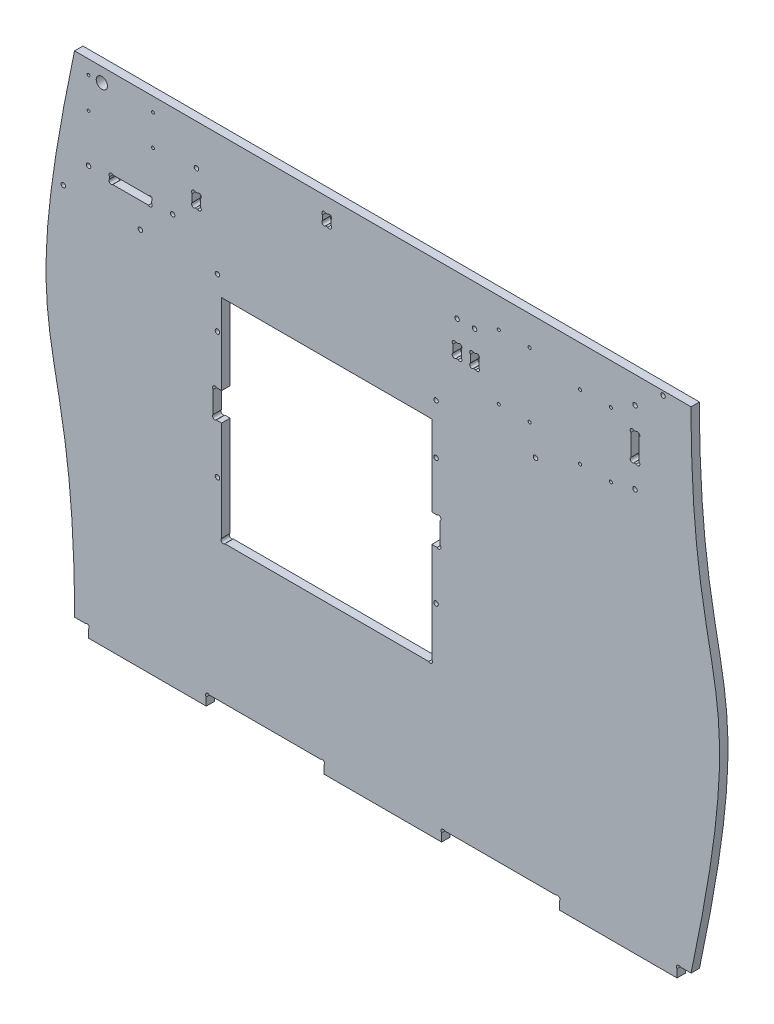
SolidWorks part; units mm, degrees
ref_plane "Plan de face" through (0, 0, 0) normal (0, 0, 1) x (1, 0, 0)
ref_plane "Plan de dessus" through (0, 0, 0) normal (0, 1, 0) x (1, 0, 0)
ref_plane "Plan de droite" through (0, 0, 0) normal (1, 0, 0) x (0, 0, -1)
sketch "Esquisse1" plane through (0, 0, 0) normal (0, 0, 1) x (1, 0, 0)
  line L0 (536.5085, 0) -> (-13.3743, 0) construction
  line L1 (0, 0) -> (84, 0)
  line L2 (0, 8) -> (-13.4384, -5.4384) construction
  line L3 (-10, 358) -> (430, 358)
  line L4 (-10, 8) -> (-2.2627, 8)
  line L5 (0, 317.0008) -> (0, 420.4252) construction
  line L6 (420, -67.8064) -> (420, 420.4252) construction
  line L7 (-58.7504, 358) -> (536.5085, 358) construction
  line L8 (-44.4443, 8) -> (504.1642, 8) construction
  line L9 (-58.7504, 183) -> (504.1642, 183) construction
  line L10 (210, -34.4525) -> (210, 403.8703) construction
  line L11 (95, 312.8184) -> (95, 62.6795) construction
  line L12 (245, 312.8184) -> (245, 77.601) construction
  line L13 (44.0199, 268) -> (294.4824, 268) construction
  line L14 (37.67, 113) -> (257.0223, 113) construction
  line L15 (170, 374.1921) -> (170, 173.0003) construction
  line L16 (377.3817, 329) -> (337.8551, 329) construction
  line L17 (-22.7237, 274) -> (398.8212, 274) construction
  line L18 (61.9408, 190.5) -> (173.6524, 190.5) construction
  line L19 (61.9408, 180.5) -> (97.9919, 180.5) construction
  line L20 (89, 328.4277) -> (89, 62.6795) construction
  line L21 (89, 180.5) -> (106.3802, 197.8802) construction
  line L22 (112.0092, 188) -> (81.9912, 188) construction
  line L23 (434.3285, 271) -> (12.2974, 271) construction
  line L24 (332.75, 372.1626) -> (332.75, 320.7373) construction
  line L25 (61.9408, 145.5) -> (97.9919, 145.5) construction
  line L26 (92, 278.6686) -> (92, 94.6559) construction
  line L27 (112.0092, 284) -> (81.9912, 284) construction
  line L28 (372.75, 339) -> (372.75, 276.9465) construction
  line L29 (91.2627, 180.5) -> (95, 180.5)
  line L30 (95, 180.5) -> (95, 109.2627)
  line L31 (95, 200.5) -> (95, 258)
  line L32 (91.2627, 200.5) -> (95, 200.5)
  line L33 (89, 198.2373) -> (89, 182.7627)
  line L34 (350.75, 339) -> (350.75, 276.9465) construction
  line L35 (174.5986, 347.4) -> (148.3113, 347.4) construction
  line L36 (321.3988, 283) -> (377.3817, 283) construction
  line L37 (251, 198.2373) -> (251, 182.7627)
  line L38 (248.7373, 200.5) -> (245, 200.5)
  line L39 (245, 200.5) -> (245, 258)
  line L40 (245, 180.5) -> (245, 109.2627)
  line L41 (248.7373, 180.5) -> (245, 180.5)
  line L42 (37.67, 107) -> (257.0223, 107) construction
  line L43 (97.2627, 107) -> (242.7373, 107)
  line L44 (84, 13.5522) -> (84, -67.8064) construction
  line L45 (168, 13.5522) -> (168, -67.8064) construction
  line L46 (126, 13.5522) -> (126, -34.4525) construction
  line L47 (84, 8) -> (114.9336, -22.9336) construction
  line L48 (86.2627, 8) -> (165.7373, 8)
  line L49 (84, 5.7373) -> (84, 0)
  line L50 (168, 5.7373) -> (168, 0)
  line L51 (252, 5.7373) -> (252, 0)
  line L52 (168, 0) -> (252, 0)
  line L53 (336, 5.7373) -> (336, 0)
  line L54 (333.7373, 8) -> (254.2627, 8)
  line L55 (336, 0) -> (420, 0)
  line L56 (-18, 278.6686) -> (-18, 232.7276) construction
  line L57 (377.3817, 339) -> (411.7088, 339) construction
  line L58 (319, 282.5821) -> (319, 262.0427) construction
  line L59 (-30, -67.8064) -> (-30, 412.0672) construction
  line L60 (-10, 374.1921) -> (-10, -22.9336) construction
  line L61 (-20, 196.1893) -> (-20, 121.5026) construction
  line L62 (314.75, 339) -> (314.75, 276.9465) construction
  line L63 (-44.4443, 158) -> (15.8377, 158) construction
  line L64 (-58.7504, 208) -> (12.2974, 208) construction
  line L65 (292.75, 339) -> (292.75, 276.9465) construction
  line L66 (420, 0) -> (420, 5.7373)
  line L67 (422.2627, 8) -> (430, 8)
  line L68 (420, 8) -> (436.9027, -8.9027) construction
  line L69 (0, 5.7373) -> (0, 0)
  line L70 (401.9564, 323) -> (377.3817, 323) construction
  line L71 (377.3817, 303) -> (411.7088, 303) construction
  line L72 (377.3817, 287) -> (411.7088, 287) construction
  line L73 (382.8422, 313) -> (400.9535, 313) construction
  line L74 (37, 278.6686) -> (37, 252.4818) construction
  line L75 (387, 265.7773) -> (387, 372.1626) construction
  line L76 (393, 297.0582) -> (393, 363.8775) construction
  line L77 (387, 303) -> (396.2728, 312.2728) construction
  line L78 (389.2627, 323) -> (390.7373, 323)
  line L79 (393, 320.7373) -> (393, 305.2627)
  line L80 (430, 429.0413) -> (430, 142.9931) construction
  line L81 (390, 390.6781) -> (390, 264.55) construction
  line L82 (390.7373, 303) -> (389.2627, 303)
  line L83 (387, 305.2627) -> (387, 320.7373)
  line L84 (95, 107) -> (145.4679, 157.4679) construction
  line L85 (260, 337.0041) -> (260, 279.8872) construction
  line L86 (266, 337.0041) -> (266, 279.8872) construction
  line L87 (282.4812, 304) -> (255.0884, 304) construction
  line L88 (410, 378.6044) -> (410, 349.1334) construction
  line L89 (404.9347, 355) -> (382.8422, 355) construction
  line L90 (-13.3743, 348) -> (53.3664, 348) construction
  line L91 (46, 356.0435) -> (46, 317.0008) construction
  line L92 (9.5, 333.4562) -> (9.5, 351.4952) construction
  line L93 (-13.3743, 326) -> (53.3664, 326) construction
  line L94 (329.6726, 291) -> (286.3117, 291) construction
  line L95 (286.3117, 337) -> (329.6726, 337) construction
  line L96 (257.0223, 258) -> (81.9912, 258) construction
  line L97 (263, 294.766) -> (263, 346.378) construction
  line L98 (282.4812, 309) -> (255.0884, 309) construction
  line L99 (260, 304) -> (273.0008, 317.0008) construction
  line L100 (282.4812, 329) -> (255.0884, 329) construction
  line L101 (262.2627, 314) -> (263.7373, 314)
  line L102 (260, 311.7373) -> (260, 306.2627)
  line L103 (262.2627, 304) -> (263.7373, 304)
  line L104 (266, 306.2627) -> (266, 311.7373)
  line L105 (74, 306.2627) -> (74, 311.7373)
  line L106 (77.7373, 304) -> (76.2627, 304)
  line L107 (80, 311.7373) -> (80, 306.2627)
  line L108 (77.7373, 314) -> (76.2627, 314)
  line L109 (269.25, 337.0041) -> (269.25, 319.1195) construction
  line L110 (272.5, 306.2627) -> (272.5, 311.7373)
  line L111 (276.2373, 304) -> (274.7627, 304)
  line L112 (278.5, 311.7373) -> (278.5, 306.2627)
  line L113 (276.2373, 314) -> (274.7627, 314)
  line L114 (-27.2619, 295) -> (81.9912, 295) construction
  line L115 (73, 282.5821) -> (73, 374.1921) construction
  line L116 (-27.2619, 289) -> (81.9912, 289) construction
  line L117 (30, 312.8686) -> (30, 284) construction
  line L118 (45, 309) -> (45, 284) construction
  line L119 (45, 289) -> (31.8516, 302.1484) construction
  line L120 (60, 309) -> (60, 284) construction
  line L121 (68.4592, 292) -> (52.4653, 292) construction
  line L122 (15, 292.7373) -> (15, 291.2627)
  line L123 (17.2627, 295) -> (42.7373, 295)
  line L124 (17.2627, 289) -> (42.7373, 289)
  line L125 (45, 292.7373) -> (45, 291.2627)
  line L126 (245, 258) -> (95, 258)
  line L127 (174.5986, 343.4) -> (148.3113, 343.4) construction
  line L128 (173, 349.9561) -> (173, 335.0973) construction
  line L129 (173, 347.4) -> (162.419, 336.819) construction
  line L130 (170.7373, 339.4) -> (169.2627, 339.4)
  line L131 (167, 341.6627) -> (167, 345.1373)
  line L132 (169.2627, 347.4) -> (170.7373, 347.4)
  line L133 (173, 345.1373) -> (173, 341.6627)
  circle A0 centre (92, 271) radius 1.6
  circle A1 centre (248, 271) radius 1.6
  arc A2 (89, 182.7627) -> (91.2627, 180.5) centre (90.1314, 181.6314) ccw
  circle A3 centre (92, 145.5) radius 1.6
  arc A4 (89, 198.2373) -> (91.2627, 200.5) centre (90.1314, 199.3686) cw
  circle A5 centre (92, 235.5) radius 1.6
  circle A6 centre (372.75, 329) radius 1.1
  circle A7 centre (350.75, 329) radius 1.1
  circle A8 centre (248, 235.5) radius 1.6
  arc A9 (251, 198.2373) -> (248.7373, 200.5) centre (249.8686, 199.3686) ccw
  circle A10 centre (248, 145.5) radius 1.6
  arc A11 (251, 182.7627) -> (248.7373, 180.5) centre (249.8686, 181.6314) cw
  arc A12 (86.2627, 8) -> (84, 5.7373) centre (85.1314, 6.8686) ccw
  arc A13 (165.7373, 8) -> (168, 5.7373) centre (166.8686, 6.8686) cw
  arc A14 (254.2627, 8) -> (252, 5.7373) centre (253.1314, 6.8686) ccw
  arc A15 (333.7373, 8) -> (336, 5.7373) centre (334.8686, 6.8686) cw
  circle A16 centre (350.75, 283) radius 1.1
  circle A17 centre (319, 271) radius 1.6
  circle A18 centre (-18, 271) radius 1.6
  arc A19 (422.2627, 8) -> (420, 5.7373) centre (421.1314, 6.8686) ccw
  arc A20 (0, 5.7373) -> (-2.2627, 8) centre (-1.1314, 6.8686) ccw
  arc A21 (387, 305.2627) -> (389.2627, 303) centre (388.1314, 304.1314) ccw
  arc A22 (393, 305.2627) -> (390.7373, 303) centre (391.8686, 304.1314) cw
  arc A23 (393, 320.7373) -> (390.7373, 323) centre (391.8686, 321.8686) ccw
  arc A24 (387, 320.7373) -> (389.2627, 323) centre (388.1314, 321.8686) cw
  circle A25 centre (37, 271) radius 1.6
  arc A26 (95, 109.2627) -> (97.2627, 107) centre (96.1314, 108.1314) ccw
  circle A27 centre (390, 339) radius 1.6
  circle A28 centre (390, 287) radius 1.6
  arc A29 (245, 109.2627) -> (242.7373, 107) centre (243.8686, 108.1314) cw
  arc A30 (260, 306.2627) -> (262.2627, 304) centre (261.1314, 305.1314) ccw
  arc A31 (266, 306.2627) -> (263.7373, 304) centre (264.8686, 305.1314) cw
  arc A32 (266, 311.7373) -> (263.7373, 314) centre (264.8686, 312.8686) ccw
  circle A33 centre (410, 355) radius 1.6
  circle A34 centre (9.5, 348) radius 4
  circle A35 centre (46, 348) radius 1
  circle A36 centre (0, 348) radius 1
  circle A37 centre (0, 326) radius 1
  circle A38 centre (46, 326) radius 1
  circle A39 centre (372.75, 283) radius 1.1
  circle A40 centre (314.75, 337) radius 1.1
  circle A41 centre (292.75, 337) radius 1.1
  circle A42 centre (292.75, 291) radius 1.1
  circle A43 centre (314.75, 291) radius 1.1
  arc A44 (260, 311.7373) -> (262.2627, 314) centre (261.1314, 312.8686) cw
  circle A45 centre (263, 329) radius 1.6
  circle A46 centre (77, 329) radius 1.6
  arc A47 (80, 311.7373) -> (77.7373, 314) centre (78.8686, 312.8686) ccw
  arc A48 (74, 311.7373) -> (76.2627, 314) centre (75.1314, 312.8686) cw
  arc A49 (74, 306.2627) -> (76.2627, 304) centre (75.1314, 305.1314) ccw
  arc A50 (80, 306.2627) -> (77.7373, 304) centre (78.8686, 305.1314) cw
  arc A51 (278.5, 311.7373) -> (276.2373, 314) centre (277.3686, 312.8686) ccw
  arc A52 (272.5, 311.7373) -> (274.7627, 314) centre (273.6314, 312.8686) cw
  arc A53 (272.5, 306.2627) -> (274.7627, 304) centre (273.6314, 305.1314) ccw
  arc A54 (278.5, 306.2627) -> (276.2373, 304) centre (277.3686, 305.1314) cw
  circle A55 centre (275.5, 329) radius 1.6
  circle A56 centre (60, 292) radius 1.6
  arc A57 (42.7373, 289) -> (45, 291.2627) centre (43.8686, 290.1314) ccw
  arc A58 (42.7373, 295) -> (45, 292.7373) centre (43.8686, 293.8686) cw
  circle A59 centre (0, 292) radius 1.6
  arc A60 (17.2627, 295) -> (15, 292.7373) centre (16.1314, 293.8686) ccw
  arc A61 (17.2627, 289) -> (15, 291.2627) centre (16.1314, 290.1314) cw
  arc A62 (173, 345.1373) -> (170.7373, 347.4) centre (171.8686, 346.2686) ccw
  arc A63 (167, 345.1373) -> (169.2627, 347.4) centre (168.1314, 346.2686) cw
  arc A64 (173, 341.6627) -> (170.7373, 339.4) centre (171.8686, 340.5314) cw
  arc A65 (167, 341.6627) -> (169.2627, 339.4) centre (168.1314, 340.5314) ccw
  spline S0 degree 3 poles (-10, 358) (-55.762, 141.1251) (-10, 195.4586) (-10, 8) knots 0 0 0 0 1 1 1 1
  spline S2 degree 3 poles (430, 8) (475.762, 224.8749) (430, 170.5414) (430, 358) knots 0 0 0 0 1 1 1 1
  dimension "D19" = 3
  dimension "D22" = 6
  dimension "D27" = 55
  dimension "D30" = 30
  dimension "D36" = 45
  dimension "D37" = 16
  dimension "D43" = 6
  dimension "D46" = 71
  dimension "D48" = 10
  dimension "D52" = 45
  dimension "D13" = 83
  dimension "D21" = 110
  dimension "D42" = 10
  dimension "D53" = 15
  dimension "D60" = 3.25
  dimension "D61" = 6
  dimension "D68" = 22
  dimension "D16" = 54.25
  dimension "D72" = 22
  dimension "D76" = 10
  dimension "D1" = 8
  dimension "D2" = 358
  dimension "D3" = 155
  dimension "D4" = 150
  dimension "D5" = 420
  dimension "D6" = 96
  dimension "D7" = 175
  dimension "D8" = 175
  dimension "D9" = 90
  dimension "D10" = 75
  dimension "D11" = 77.5
  dimension "D12" = 10
  dimension "D14" = 6
  dimension "D15" = 6
  dimension "D17" = 35
  dimension "D18" = 3
  dimension "D20" = 45
  dimension "D23" = 84
  dimension "D24" = 42
  dimension "D25" = 42
  dimension "D26" = 45
  dimension "D28" = 210
  dimension "D29" = 19
  dimension "D31" = 20
  dimension "D32" = 10
  dimension "D33" = 150
  dimension "D34" = 150
  dimension "D35" = 45
  dimension "D38" = 20
  dimension "D39" = 16
  dimension "D40" = 40
  dimension "D41" = 20
  dimension "D44" = 3
  dimension "D45" = 45
  dimension "D47" = 3
  dimension "D49" = 22
  dimension "D50" = 46
  dimension "D51" = 9.5
  dimension "D54" = 3
  dimension "D55" = 6
  dimension "D56" = 30
  dimension "D57" = 5
  dimension "D58" = 45
  dimension "D59" = 20
  dimension "D62" = 21
  dimension "D63" = 15
  dimension "D64" = 43
  dimension "D65" = 15
  dimension "D66" = 3
  dimension "D67" = 45
  dimension "D69" = 46
  dimension "D70" = 9
  dimension "D71" = 18
  dimension "D73" = 46
  dimension "D74" = 8
  dimension "D75" = 18
  dimension "D77" = 4
  dimension "D78" = 3
  dimension "D79" = 10.6
  dimension "D80" = 45
extrude "Boss.-Extru.1" add sketch "Esquisse1" along normal blind 6
